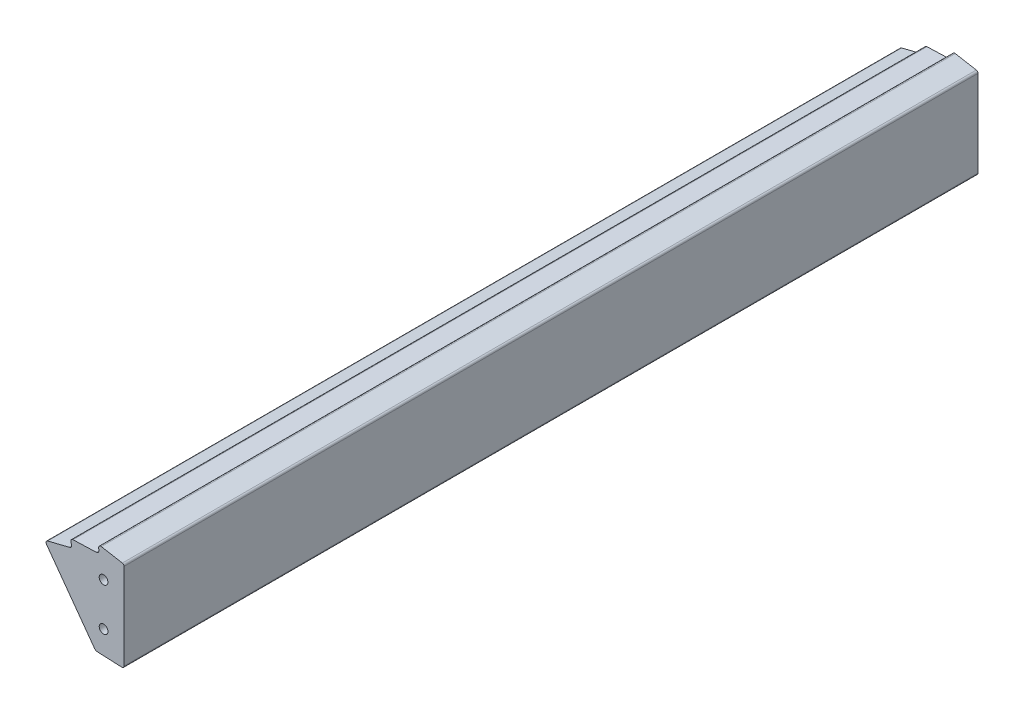
SolidWorks part; units mm, degrees
material "ladder carbon corrected"
ref_plane "Front Plane" through (0, 0, 0) normal (0, 0, 1) x (1, 0, 0)
ref_plane "Top Plane" through (0, 0, 0) normal (0, 1, 0) x (1, 0, 0)
ref_plane "Right Plane" through (0, 0, 0) normal (1, 0, 0) x (0, 0, -1)
sketch "Sketch1" plane through (0, 0, 0) normal (0, 0, 1) x (1, 0, 0)
  line L0 (-16.9638, 26.5341) -> (-2.5682, 25.8793)
  line L1 (-46.8997, 66.2532) -> (-18.7351, 27.4879)
  line L2 (-46.0481, 68.5905) -> (-33.2024, 71.7845)
  line L3 (-31.1768, 76.652) -> (-17.552, 77.119)
  line L4 (-1, 77.8014) -> (-1, 27.3777)
  line L5 (-14.5587, 81.459) -> (-2.2386, 79.2785)
  line L6 (0, 0) -> (-21.3966, 104.6618) construction
  line L7 (0, 0) -> (-41.6883, 95.6295) construction
  line L8 (-52.6003, 66.9614) -> (-33.9676, 71.5943) construction
  line L9 (-1, 70.6811) -> (-1, 38.7624) construction
  line L10 (-37.5288, 76.4343) -> (-18.3401, 77.092) construction
  line L11 (-21.1016, 30.7452) -> (-44.2572, 62.6161) construction
  line L17 (-20.8171, 82.5667) -> (-1.9109, 79.2205) construction
  line L19 (-16.2897, 79.6815) -> (-16.1338, 78.9186)
  line L20 (-32.5005, 74.5535) -> (-32.1893, 73.8396)
  line L21 (-16.6758, 26.521) -> (2.5044, 25.6486) construction
  line L22 (-17.5784, 77.8902) -> (-17.552, 77.119) construction
  line L23 (-16.9638, 26.5341) -> (-16.9989, 25.7633) construction
  arc A0 (-33.2024, 71.7845) -> (-32.1893, 73.8396) centre (-33.5643, 73.2402) ccw
  arc A1 (-31.1768, 76.652) -> (-32.5005, 74.5535) centre (-31.1255, 75.1529) ccw
  arc A2 (-17.552, 77.119) -> (-16.1338, 78.9186) centre (-17.6034, 78.6181) ccw
  arc A3 (-14.5587, 81.459) -> (-16.2897, 79.6815) centre (-14.8201, 79.982) ccw
  arc A4 (-2.2386, 79.2785) -> (-1, 77.8014) centre (-2.5, 77.8014) cw
  arc A5 (-46.0481, 68.5905) -> (-46.8997, 66.2532) centre (-45.6861, 67.1348) ccw
  arc A6 (-16.9638, 26.5341) -> (-18.7351, 27.4879) centre (-16.8584, 28.8514) cw
  arc A7 (-1, 27.3777) -> (-2.5682, 25.8793) centre (-2.5, 27.3777) cw
  dimension "D1" = 1.5
  dimension "D2" = 1.5
extrude "Extrude-Thin1" add sketch "Sketch1" along normal blind 137.5002 and the other way blind 213.5 thin thin type one direction reverse wall 0.27
sketch "Sketch2" plane through (0, 0, 0) normal (0, 0, 1) x (1, 0, 0)
  line L0 (-46.6812, 66.4119) -> (-18.5167, 27.6466) construction
  line L1 (-16.9515, 26.8038) -> (-2.5559, 26.149) construction
  line L2 (-1.27, 27.3777) -> (-1.27, 77.8014) construction
  line L3 (-46.6812, 66.4119) -> (-18.5167, 27.6466)
  line L4 (-16.9515, 26.8038) -> (-2.5559, 26.149)
  line L5 (-1.27, 27.3777) -> (-1.27, 77.8014)
  line L6 (-46.6812, 66.4119) -> (-46.7308, 66.48)
  line L31 (-1.27, 77.9505) -> (-1.27, 77.8014)
  line L36 (-2.2638, 79.1357) -> (-14.584, 81.3162)
  line L37 (-16.1477, 79.7106) -> (-15.9917, 78.9476)
  line L38 (-17.547, 76.9741) -> (-31.1719, 76.5071)
  line L39 (-32.3676, 74.6114) -> (-32.0564, 73.8976)
  line L40 (-33.1674, 71.6438) -> (-46.0131, 68.4498)
  line L41 (-2.2638, 79.1357) -> (-14.584, 81.3162)
  line L42 (-16.1477, 79.7106) -> (-15.9917, 78.9476)
  line L43 (-17.547, 76.9741) -> (-31.1719, 76.5071)
  line L44 (-32.3676, 74.6114) -> (-32.0564, 73.8976)
  line L45 (-33.1674, 71.6438) -> (-46.0131, 68.4498)
  arc A0 (-18.5167, 27.6466) -> (-16.9515, 26.8038) centre (-16.8584, 28.8514) ccw construction
  arc A1 (-2.5559, 26.149) -> (-1.27, 27.3777) centre (-2.5, 27.3777) ccw construction
  arc A2 (-18.5167, 27.6466) -> (-16.9515, 26.8038) centre (-16.8584, 28.8514) ccw
  arc A3 (-2.5559, 26.149) -> (-1.27, 27.3777) centre (-2.5, 27.3777) ccw
  arc A24 (-46.0131, 68.4498) -> (-46.7308, 66.48) centre (-45.7081, 67.2231) ccw
  arc A25 (-2.2638, 79.1357) -> (-1.27, 77.9505) centre (-2.4736, 77.9505) cw
  arc A28 (-14.584, 81.3162) -> (-16.1477, 79.7106) centre (-14.8201, 79.982) ccw
  arc A29 (-17.547, 76.9741) -> (-15.9917, 78.9476) centre (-17.6034, 78.6181) ccw
  arc A30 (-31.1719, 76.5071) -> (-32.3676, 74.6114) centre (-31.1255, 75.1529) ccw
  arc A31 (-33.1674, 71.6438) -> (-32.0564, 73.8976) centre (-33.5643, 73.2402) ccw
  arc A32 (-14.584, 81.3162) -> (-16.1477, 79.7106) centre (-14.8201, 79.982) ccw
  arc A33 (-17.547, 76.9741) -> (-15.9917, 78.9476) centre (-17.6034, 78.6181) ccw
  arc A34 (-31.1719, 76.5071) -> (-32.3676, 74.6114) centre (-31.1255, 75.1529) ccw
  arc A35 (-33.1674, 71.6438) -> (-32.0564, 73.8976) centre (-33.5643, 73.2402) ccw
  dimension "D1" = 0.125
extrude "Boss-Extrude1" add sketch "Sketch2" along normal offset from surface 75 and the other way offset from surface (288.5 mm away) 75 separate body up to face at (-20.5831, 63.3356, 137.5002) offset beyond the face yes other way up to face at (-20.4978, 63.2944, -213.5)
delete or keep bodies "Body-Delete1" type delete bodies bodies 101
sketch "Sketch3" plane through (0, 0, 0) normal (1, 0, 0) x (0, 0, -1)
  line L0 (-212.0001, 102.6641) -> (287.9999, 102.6641)
  line L1 (-212.0001, 102.6641) -> (-212.0001, 2.6641)
  line L2 (287.9999, 102.6641) -> (287.9999, 2.6641)
  line L3 (-212.0001, 2.6641) -> (287.9999, 2.6641)
  line L4 (-212.5002, 52.6641) -> (-212.0001, 52.6641) construction
  line L5 (-212.5002, 27.3777) -> (-212.5002, 77.9505) construction
  line L6 (288.5, 52.6641) -> (287.9999, 52.6641) construction
  line L7 (288.5, 77.9505) -> (288.5, 27.3777) construction
  dimension "D1" = 500
  dimension "D2" = 100
extrude "Cut-Extrude1" cut sketch "Sketch3" against normal through all flip side to cut
hole_wizard "1/4-20 Tapped Hole1" positions "3DSketch1" profile "Sketch4" tap size "1/4-20" standard "ANSI Inch"
sketch3d "3DSketch1"
  line L0 (-13.27, 65.1641, -287.9999) -> (-13.27, 40.1641, -287.9999)
  line L1 (-13.27, 40.1641, -287.9999) -> (-13.27, 40.1641, 212.0001)
  line L2 (-13.27, 40.1641, 212.0001) -> (-13.27, 65.1641, 212.0001)
  line L3 (-13.27, 65.1641, 212.0001) -> (-13.27, 65.1641, -287.9999)
  line L6 (-1.27, 27.3777, 212.0001) -> (-1.27, 77.9505, 212.0001) construction
  line L8 (-13.27, 52.6641, -287.9999) -> (-1.27, 52.6641, -287.9999) construction
  line L10 (-1.27, 77.9505, -287.9999) -> (-1.27, 27.3777, -287.9999) construction
  point P0 (-13.27, 65.1641, 212.0001)
  point P2 (-13.27, 40.1641, 212.0001)
  point P4 (-13.27, 65.1641, -287.9999)
  point P6 (-13.27, 40.1641, -287.9999)
  dimension "D1" = 25
  dimension "D2" = 12
sketch "Sketch4" plane through (-13.27, 65.1641, 212.0001) normal (1, 0, 0) x (0, -1, 0)
  line L0 (0, 0) -> (0, 18.0438)
  line L1 (0, 18.0438) -> (2.5527, 16.51)
  line L2 (2.5527, 16.51) -> (2.5527, 0)
  line L5 (2.5527, 0) -> (0, 0)
  line L10 (0, 18.0438) -> (-2.5527, 16.51) construction
  line L11 (0, -6.35) -> (0, 107.95) construction
  dimension "Tap Drill Dia." = 5.1054
  dimension "Tap Drill Depth" = 16.51
  dimension "Drill Angle" = 118
cosmetic thread "Hole Thread1" parameters "D1"=12.7, "D2"=6.35
cosmetic thread "Hole Thread2" parameters "D1"=12.7, "D2"=6.35
cosmetic thread "Hole Thread3" parameters "D1"=12.7, "D2"=6.35
cosmetic thread "Hole Thread4" parameters "D1"=12.7, "D2"=6.35
